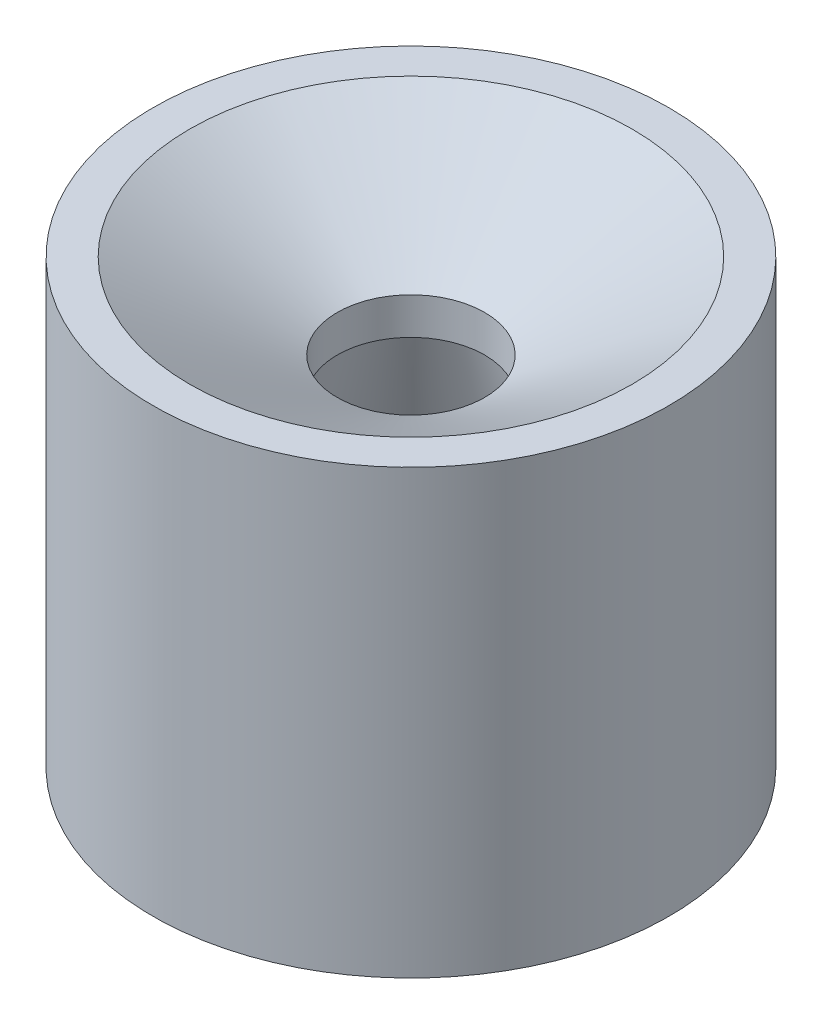
SolidWorks part; units mm, degrees
material "C (Graphite)"
ref_plane "Front Plane" through (0, 0, 0) normal (0, 0, 1) x (1, 0, 0)
ref_plane "Top Plane" through (0, 0, 0) normal (0, 1, 0) x (1, 0, 0)
ref_plane "Right Plane" through (0, 0, 0) normal (1, 0, 0) x (0, 0, -1)
sketch "Sketch1" plane through (0, 0, 0) normal (0, 0, 1) x (1, 0, 0)
  line L0 (0, 0) -> (0, 76.2) construction
  line L1 (0, 0) -> (-44.45, 0) construction
  line L2 (-44.45, 0) -> (-44.45, 76.2)
  line L4 (-12.7, 61.5353) -> (-12.7, 55.1853)
  line L5 (-12.7, 55.1853) -> (-28.321, 0)
  line L6 (-28.321, 0) -> (-44.45, 0)
  line L7 (-44.45, 76.2) -> (-38.1, 76.2)
  line L8 (-38.1, 76.2) -> (-12.7, 61.5353)
  point P3 (0, 0)
  dimension "D1" = 76.2
  dimension "D2" = 28.321
  dimension "D3" = 12.7
  dimension "D4" = 6.35
  dimension "D5" = 44.45
  dimension "D6" = 6.35
  dimension "D7" = 30
  dimension "D8" = 16.129
revolve "Revolve1" add sketch "Sketch1" angle 360 about L0
